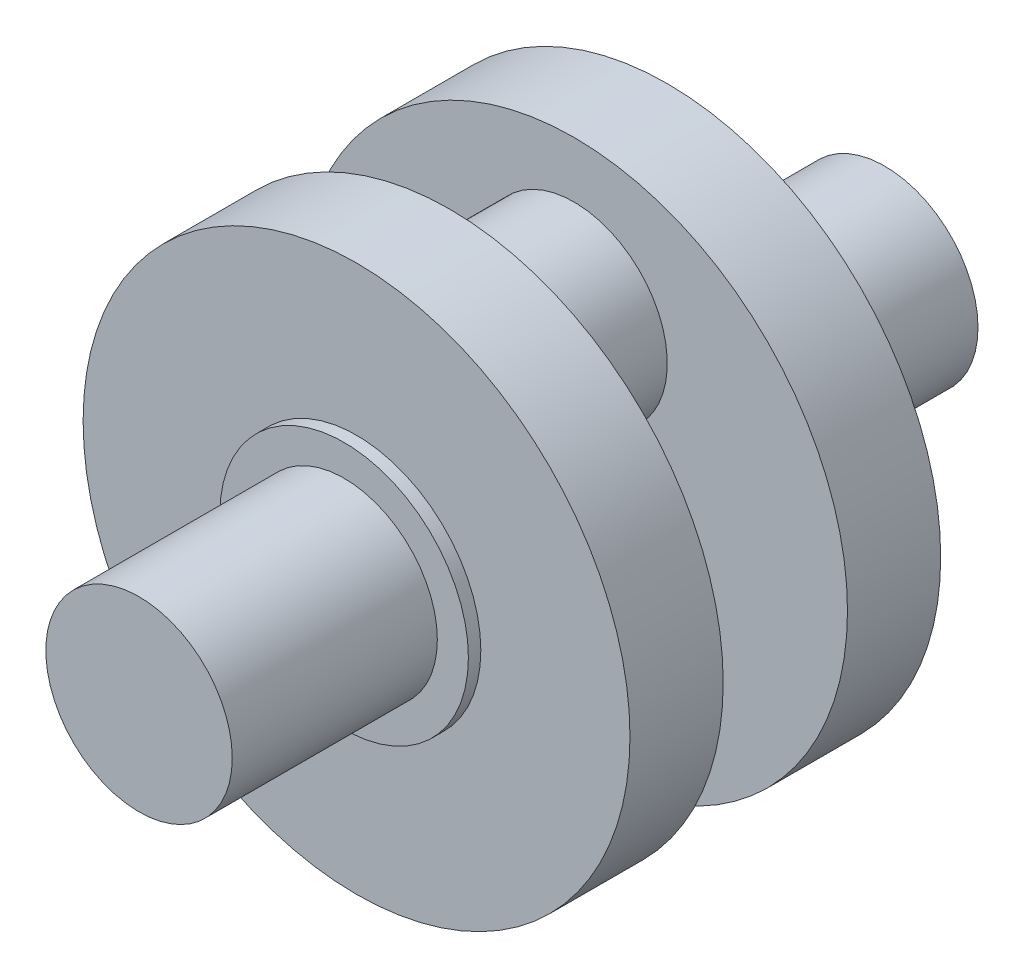
SolidWorks part; units mm, degrees
ref_plane "Płaszczyzna przednia" through (0, 0, 0) normal (0, 0, 1) x (1, 0, 0)
ref_plane "Płaszczyzna górna" through (0, 0, 0) normal (0, 1, 0) x (1, 0, 0)
ref_plane "Płaszczyzna prawa" through (0, 0, 0) normal (1, 0, 0) x (0, 0, -1)
sketch "Szkic2" plane through (0, 0, 0) normal (0, 0, 1) x (1, 0, 0)
  circle A0 centre (0, 0) radius 15
  dimension "D1" = 30
extrude "Dodanie-wyciągnięcie1" add sketch "Szkic2" along normal blind 33
sketch "Szkic3" plane through (0, 0, 0) normal (0, 0, 1) x (1, 0, 0)
  circle A0 centre (0, 0) radius 20
  dimension "D1" = 40
extrude "Dodanie-wyciągnięcie2" add sketch "Szkic3" against normal blind 2
sketch "Szkic4" plane through (0, 0, -2) normal (0, 0, -1) x (-1, 0, 0)
  circle A0 centre (0, 0) radius 44
  dimension "D1" = 88
extrude "Dodanie-wyciągnięcie3" add sketch "Szkic4" along normal blind 15
sketch "Szkic5" plane through (0, 0, -17) normal (0, 0, -1) x (-1, 0, 0)
  circle A0 centre (0, 20) radius 15
  dimension "D2" = 30
  dimension "D1" = 20
extrude "Dodanie-wyciągnięcie4" add sketch "Szkic5" along normal blind 10
mirror "Lustro1" about plane through (0, 20, -27) normal (0, 0, -1) of bodies 104
